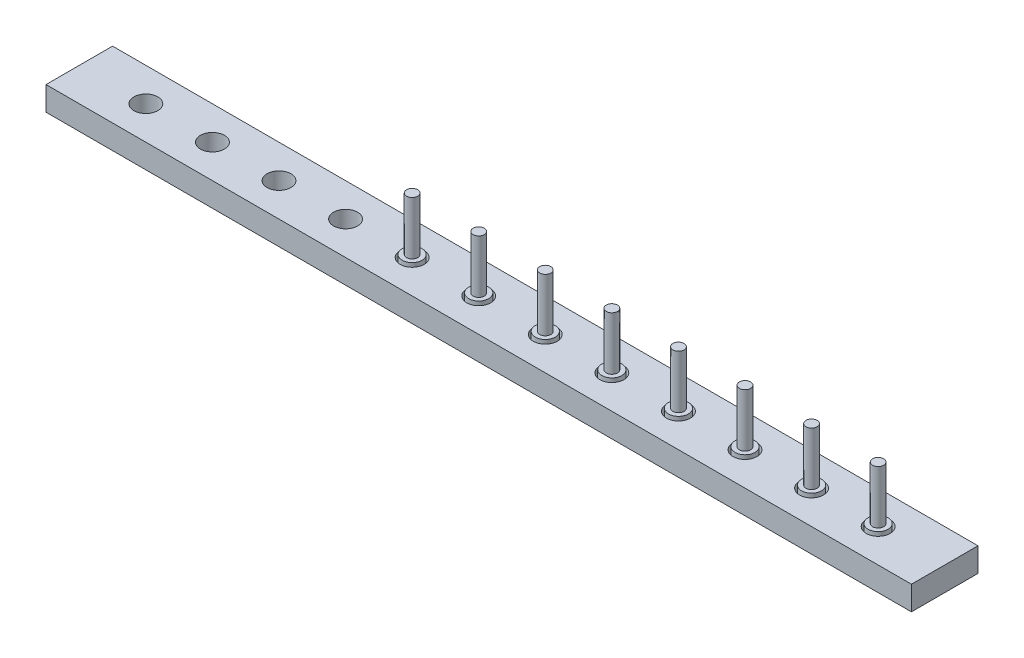
SolidWorks part; units mm, degrees
ref_plane "Front Plane" through (0, 0, 0) normal (0, 0, 1) x (1, 0, 0)
ref_plane "Top Plane" through (0, 0, 0) normal (0, 1, 0) x (1, 0, 0)
ref_plane "Right Plane" through (0, 0, 0) normal (1, 0, 0) x (0, 0, -1)
sketch "Sketch1" plane through (0, 0, 0) normal (0, 1, 0) x (1, 0, 0)
  line L1 (-1625, -125) -> (1625, -125)
  line L2 (-1625, -125) -> (-1625, 125)
  line L3 (-1625, 125) -> (1625, 125)
  line L4 (1625, -125) -> (1625, 125)
  line L5 (-1625, -125) -> (1625, 125) construction
  line L6 (-1625, 125) -> (1625, -125) construction
  point P0 (0, 0)
  dimension "D1" = 3250
  dimension "D2" = 250
extrude "Boss-Extrude1" add sketch "Sketch1" along normal blind 90
sketch "Sketch2" plane through (0, 90, 0) normal (0, 1, 0) x (1, 0, 0)
  line L0 (-1625, 0) -> (1625, 0) construction
  line L1 (-1625, 125) -> (-1625, -125) construction
  line L2 (1625, -125) -> (1625, 125) construction
  circle A0 centre (-1375, 0) radius 45
  circle A1 centre (-1125, 0) radius 45
  circle A2 centre (-875, 0) radius 45
  circle A3 centre (-625, 0) radius 45
  circle A4 centre (-375, 0) radius 45
  circle A5 centre (-125, 0) radius 45
  circle A6 centre (125, 0) radius 45
  circle A7 centre (375, 0) radius 45
  circle A8 centre (625, 0) radius 45
  circle A9 centre (875, 0) radius 45
  circle A10 centre (1125, 0) radius 45
  circle A11 centre (1375, 0) radius 45
  dimension "D1" = 90
  dimension "D2" = 250
  dimension "D4" = 2750
  dimension "D3" = 12
extrude "Cut-Extrude1" cut sketch "Sketch2" against normal blind 100
sketch "Sketch3" plane through (0, 0, 0) normal (0, -1, 0) x (1, 0, 0)
  line L0 (-875, 0) -> (1375, 0) construction
  circle A2 centre (-375, 0) radius 37.5
  circle A3 centre (-125, 0) radius 37.5
  circle A4 centre (125, 0) radius 37.5
  circle A5 centre (375, 0) radius 37.5
  circle A6 centre (625, 0) radius 37.5
  circle A7 centre (875, 0) radius 37.5
  circle A8 centre (1125, 0) radius 37.5
  circle A9 centre (1375, 0) radius 37.5
  dimension "D1" = 75
  dimension "D3" = 250
  dimension "D2" = 1750
extrude "Boss-Extrude2" add sketch "Sketch3" against normal blind 100 separate body
sketch "Sketch5" plane through (0, 100, 0) normal (0, 1, 0) x (1, 0, 0)
  circle A0 centre (-375, 0) radius 21
  circle A1 centre (-125, 0) radius 21
  circle A2 centre (125, 0) radius 21
  circle A3 centre (375, 0) radius 21
  circle A4 centre (625, 0) radius 21
  circle A5 centre (875, 0) radius 21
  circle A6 centre (1125, 0) radius 21
  circle A7 centre (1375, 0) radius 21
  dimension "D1" = 42
  dimension "D3" = 1750
  dimension "D2" = 8
extrude "Boss-Extrude3" add sketch "Sketch5" along normal blind 200
